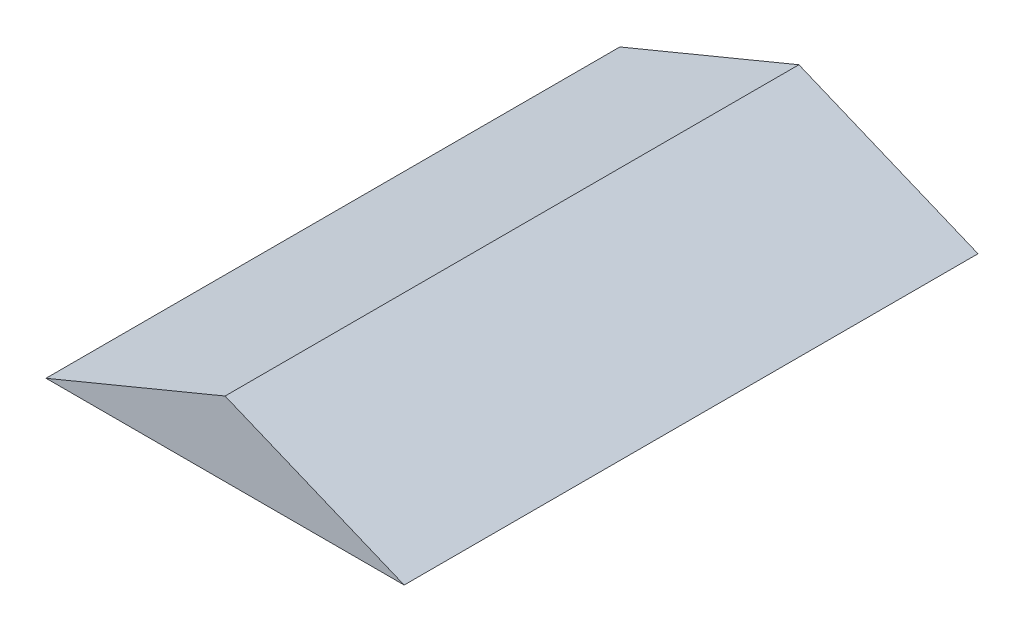
SolidWorks part; units mm, degrees
ref_plane "前基準面" through (0, 0, 0) normal (0, 0, 1) x (1, 0, 0)
ref_plane "上基準面" through (0, 0, 0) normal (0, 1, 0) x (1, 0, 0)
ref_plane "右基準面" through (0, 0, 0) normal (1, 0, 0) x (0, 0, -1)
sketch "草圖1" plane through (0, 0, 0) normal (0, 0, 1) x (1, 0, 0)
  line L0 (-25.3615, -17.6144) -> (24.6385, -17.6144)
  line L1 (24.6385, -17.6144) -> (-0.3623, -7.2644)
  line L2 (-0.3623, -7.2644) -> (-25.3615, -17.6144)
  point P2 (0, -7.1144)
  dimension "D1" = 50
  dimension "D2" = 10.35
  dimension "D3" = 22.49
extrude "填料-伸長1" add sketch "草圖1" along normal blind 80.1
